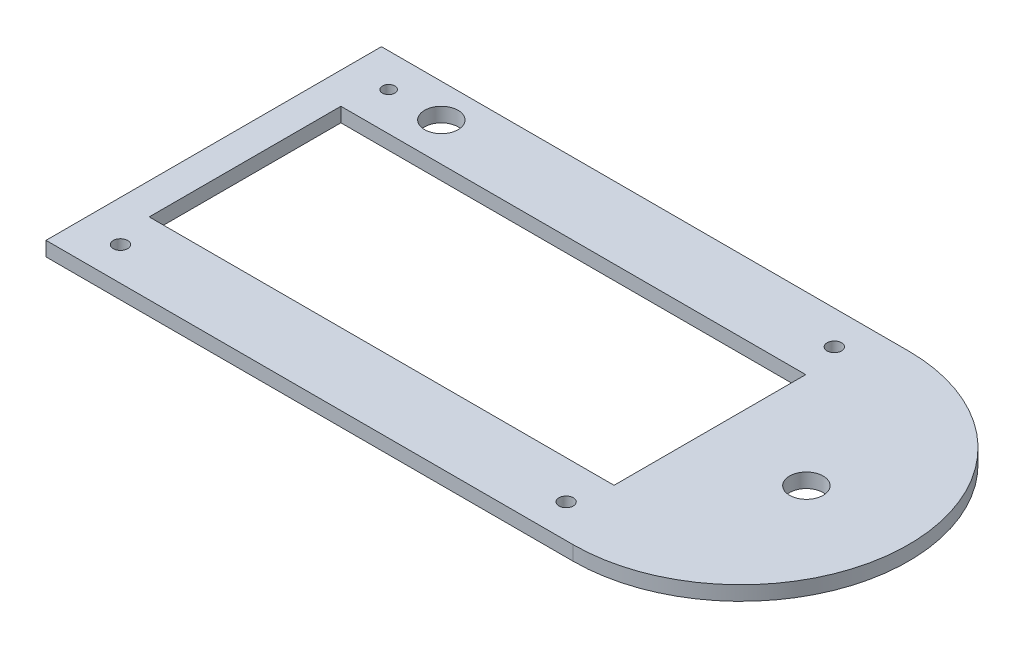
SolidWorks part; units mm, degrees
ref_plane "Front Plane" through (0, 0, 0) normal (0, 0, 1) x (1, 0, 0)
ref_plane "Top Plane" through (0, 0, 0) normal (0, 1, 0) x (1, 0, 0)
ref_plane "Right Plane" through (0, 0, 0) normal (1, 0, 0) x (0, 0, -1)
sketch "Sketch1" plane through (0, 0, 0) normal (0, 1, 0) x (1, 0, 0)
  line L1 (-67.4317, 21.979) -> (42.5683, 21.979)
  line L2 (-67.4317, 21.979) -> (-67.4317, -48.021)
  line L3 (-67.4317, -48.021) -> (42.5683, -48.021)
  line L5 (-60.8951, 6.979) -> (36.1049, 6.979)
  line L6 (-60.8951, 6.979) -> (-60.8951, -33.021)
  line L7 (-60.8951, -33.021) -> (36.1049, -33.021)
  line L8 (36.1049, 6.979) -> (36.1049, -33.021)
  circle A0 centre (-58.9317, 14.979) radius 1.3
  arc A1 (42.5683, 21.979) -> (42.5683, -48.021) centre (42.5683, -13.021) cw
  circle A2 centre (34.0683, 14.979) radius 1.5
  circle A3 centre (-58.8951, -41.021) radius 1.5
  circle A4 centre (34.1049, -41.021) radius 1.5
  circle A5 centre (56.2429, -13.021) radius 3.5
  circle A6 centre (-47.9317, 14.979) radius 3.5
  dimension "D5" = 93
  dimension "D6" = 3
  dimension "D7" = 56
  dimension "D8" = 7
  dimension "D9" = 8.5
  dimension "D10" = 8
  dimension "D11" = 3
  dimension "D12" = 93
  dimension "D13" = 56
  dimension "D14" = 7
  dimension "D16" = 7
  dimension "D17" = 11
  dimension "D18" = 7
  dimension "D1" = 40
  dimension "D2" = 97
  dimension "D3" = 110
  dimension "D4" = 70
  dimension "D15" = 2
extrude "Boss-Extrude1" add sketch "Sketch1" along normal blind 3
